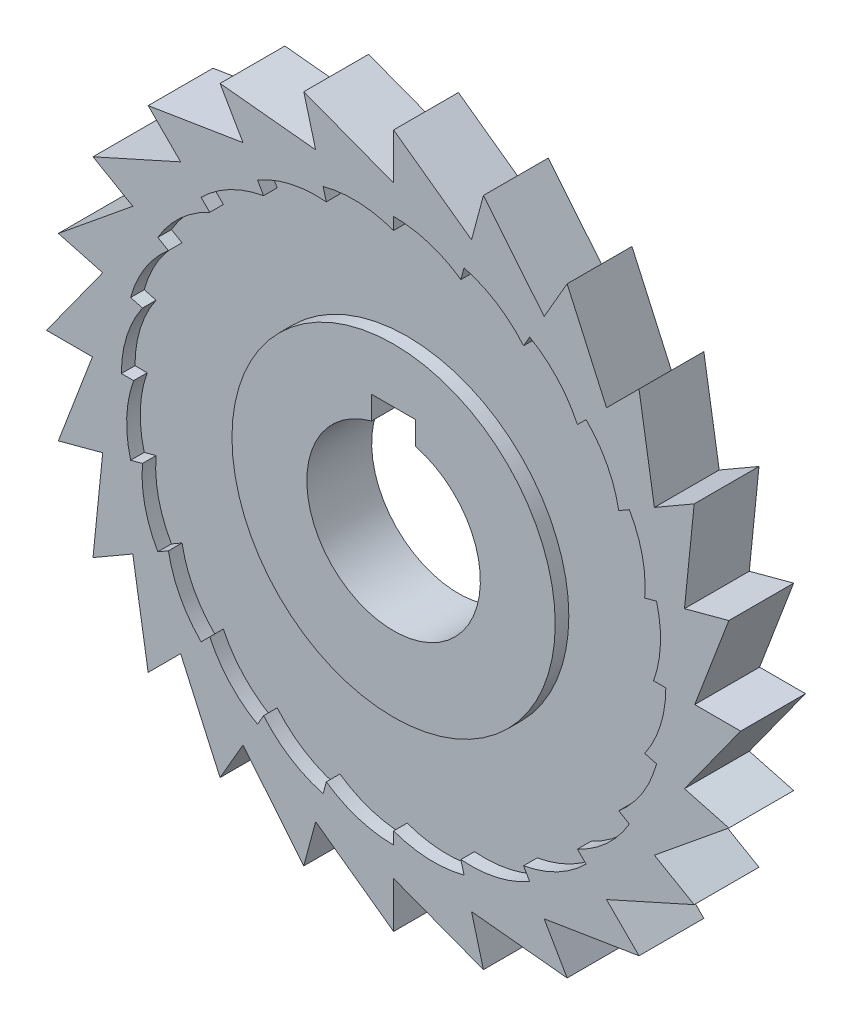
SolidWorks part; units mm, degrees
ref_plane "Alzado" through (0, 0, 0) normal (0, 0, 1) x (1, 0, 0)
ref_plane "Planta" through (0, 0, 0) normal (0, 1, 0) x (1, 0, 0)
ref_plane "Vista lateral" through (0, 0, 0) normal (1, 0, 0) x (0, 0, -1)
sketch "Croquis1" plane through (0, 0, 0) normal (0, 0, 1) x (1, 0, 0)
  line L1 (-3.25, 15.75) -> (3.25, 15.75)
  line L2 (-3.25, 15.75) -> (-3.25, 12.3288)
  line L3 (3.25, 15.75) -> (3.25, 12.3288)
  arc A0 (-3.25, 12.3288) -> (3.25, 12.3288) centre (0, 0) ccw
  circle A1 centre (0, 0) radius 23.75
  circle A2 centre (0, 0) radius 40
  point P9 (0, 15.75)
  dimension "D1" = 25.5
  dimension "D2" = 47.5
  dimension "D3" = 80
  dimension "D4" = 6.5
extrude "Saliente-Extruir1" add sketch "Croquis1" along normal blind 5.525 contours A1 A0 L2 L1 L3 | A2 A1
ref_plane "Plano1" through (0, 0, 2.7625) normal (0, 0, 1) x (1, 0, 0)
sketch "Croquis3" plane through (0, 0, 2.7625) normal (0, 0, 1) x (1, 0, 0)
  line L0 (-3.25, 15.75) -> (-3.25, 12.3288)
  line L1 (-3.25, 15.75) -> (3.25, 15.75)
  line L2 (3.25, 15.75) -> (3.25, 12.3288)
  arc A0 (-3.25, 12.3288) -> (3.25, 12.3288) centre (0, 0) ccw
  circle A1 centre (0, 0) radius 23.75
  dimension "D1" = 47.5
extrude "Saliente-Extruir3" add sketch "Croquis3" along normal blind 4.7625 and the other way blind 4.7625 contours A1 | A0 L2 L1 L0
ref_plane "Plano3" through (0, 0, 2.7625) normal (0, 0, 1) x (1, 0, 0)
sketch "Croquis5" plane through (0, 0, 2.7625) normal (0, 0, 1) x (1, 0, 0)
  line L0 (0, 40) -> (0, 51)
  line L1 (0, 38.2) -> (0, 40)
  line L2 (0, 38.2) -> (0, 63.7631) construction
  line L3 (9.8869, 36.8984) -> (11.4527, 42.7422)
  line L4 (19.1, 33.0822) -> (22.125, 38.3216)
  line L5 (13.1998, 49.2622) -> (22.125, 38.3216)
  line L6 (10.3528, 38.637) -> (13.1998, 49.2622)
  line L7 (27.0115, 27.0115) -> (31.2895, 31.2895)
  line L8 (0, 51) -> (11.4527, 42.7422)
  line L9 (25.5, 44.1673) -> (31.2895, 31.2895)
  line L10 (20, 34.641) -> (25.5, 44.1673)
  line L11 (33.0822, 19.1) -> (38.3216, 22.125)
  line L12 (36.0624, 36.0624) -> (38.3216, 22.125)
  line L13 (28.2843, 28.2843) -> (36.0624, 36.0624)
  line L14 (36.8984, 9.8869) -> (42.7422, 11.4527)
  line L15 (44.1673, 25.5) -> (42.7422, 11.4527)
  line L16 (34.641, 20) -> (44.1673, 25.5)
  line L17 (38.2, 0) -> (44.25, 0)
  line L18 (49.2622, 13.1998) -> (44.25, 0)
  line L19 (38.637, 10.3528) -> (49.2622, 13.1998)
  line L20 (36.8984, -9.8869) -> (42.7422, -11.4527)
  line L21 (51, 0) -> (42.7422, -11.4527)
  line L22 (40, 0) -> (51, 0)
  line L23 (33.0822, -19.1) -> (38.3216, -22.125)
  line L24 (49.2622, -13.1998) -> (38.3216, -22.125)
  line L25 (38.637, -10.3528) -> (49.2622, -13.1998)
  line L26 (27.0115, -27.0115) -> (31.2895, -31.2895)
  line L27 (44.1673, -25.5) -> (31.2895, -31.2895)
  line L28 (34.641, -20) -> (44.1673, -25.5)
  line L29 (19.1, -33.0822) -> (22.125, -38.3216)
  line L30 (36.0624, -36.0624) -> (22.125, -38.3216)
  line L31 (28.2843, -28.2843) -> (36.0624, -36.0624)
  line L32 (9.8869, -36.8984) -> (11.4527, -42.7422)
  line L33 (25.5, -44.1673) -> (11.4527, -42.7422)
  line L34 (20, -34.641) -> (25.5, -44.1673)
  line L35 (0, -38.2) -> (0, -44.25)
  line L36 (13.1998, -49.2622) -> (0, -44.25)
  line L37 (10.3528, -38.637) -> (13.1998, -49.2622)
  line L38 (-9.8869, -36.8984) -> (-11.4527, -42.7422)
  line L39 (0, -51) -> (-11.4527, -42.7422)
  line L40 (0, -40) -> (0, -51)
  line L41 (-19.1, -33.0822) -> (-22.125, -38.3216)
  line L42 (-13.1998, -49.2622) -> (-22.125, -38.3216)
  line L43 (-10.3528, -38.637) -> (-13.1998, -49.2622)
  line L44 (-27.0115, -27.0115) -> (-31.2895, -31.2895)
  line L45 (-25.5, -44.1673) -> (-31.2895, -31.2895)
  line L46 (-20, -34.641) -> (-25.5, -44.1673)
  line L47 (-33.0822, -19.1) -> (-38.3216, -22.125)
  line L48 (-36.0624, -36.0624) -> (-38.3216, -22.125)
  line L49 (-28.2843, -28.2843) -> (-36.0624, -36.0624)
  line L50 (-36.8984, -9.8869) -> (-42.7422, -11.4527)
  line L51 (-44.1673, -25.5) -> (-42.7422, -11.4527)
  line L52 (-34.641, -20) -> (-44.1673, -25.5)
  line L53 (-38.2, 0) -> (-44.25, 0)
  line L54 (-49.2622, -13.1998) -> (-44.25, 0)
  line L55 (-38.637, -10.3528) -> (-49.2622, -13.1998)
  line L56 (-36.8984, 9.8869) -> (-42.7422, 11.4527)
  line L57 (-51, 0) -> (-42.7422, 11.4527)
  line L58 (-40, 0) -> (-51, 0)
  line L59 (-33.0822, 19.1) -> (-38.3216, 22.125)
  line L60 (-49.2622, 13.1998) -> (-38.3216, 22.125)
  line L61 (-38.637, 10.3528) -> (-49.2622, 13.1998)
  line L62 (-27.0115, 27.0115) -> (-31.2895, 31.2895)
  line L63 (-44.1673, 25.5) -> (-31.2895, 31.2895)
  line L64 (-34.641, 20) -> (-44.1673, 25.5)
  line L65 (-19.1, 33.0822) -> (-22.125, 38.3216)
  line L66 (-36.0624, 36.0624) -> (-22.125, 38.3216)
  line L67 (-28.2843, 28.2843) -> (-36.0624, 36.0624)
  line L68 (-9.8869, 36.8984) -> (-11.4527, 42.7422)
  line L69 (-25.5, 44.1673) -> (-11.4527, 42.7422)
  line L70 (-20, 34.641) -> (-25.5, 44.1673)
  line L71 (0, 38.2) -> (0, 44.25)
  line L72 (-13.1998, 49.2622) -> (0, 44.25)
  line L73 (-10.3528, 38.637) -> (-13.1998, 49.2622)
  arc A1 (0, 40) -> (9.8869, 36.8984) centre (0, 22.6913) cw
  arc A2 (10.3528, 38.637) -> (19.1, 33.0822) centre (5.8729, 21.9181) cw
  arc A3 (20, 34.641) -> (27.0115, 27.0115) centre (11.3456, 19.6512) cw
  arc A4 (28.2843, 28.2843) -> (33.0822, 19.1) centre (16.0452, 16.0452) cw
  arc A5 (34.641, 20) -> (36.8984, 9.8869) centre (19.6512, 11.3456) cw
  arc A6 (38.637, 10.3528) -> (38.2, 0) centre (21.9181, 5.8729) cw
  arc A7 (40, 0) -> (36.8984, -9.8869) centre (22.6913, 0) cw
  arc A8 (38.637, -10.3528) -> (33.0822, -19.1) centre (21.9181, -5.8729) cw
  arc A9 (34.641, -20) -> (27.0115, -27.0115) centre (19.6512, -11.3456) cw
  arc A10 (28.2843, -28.2843) -> (19.1, -33.0822) centre (16.0452, -16.0452) cw
  arc A11 (20, -34.641) -> (9.8869, -36.8984) centre (11.3456, -19.6512) cw
  arc A12 (10.3528, -38.637) -> (0, -38.2) centre (5.8729, -21.9181) cw
  arc A13 (0, -40) -> (-9.8869, -36.8984) centre (0, -22.6913) cw
  arc A14 (-10.3528, -38.637) -> (-19.1, -33.0822) centre (-5.8729, -21.9181) cw
  arc A15 (-20, -34.641) -> (-27.0115, -27.0115) centre (-11.3456, -19.6512) cw
  arc A16 (-28.2843, -28.2843) -> (-33.0822, -19.1) centre (-16.0452, -16.0452) cw
  arc A17 (-34.641, -20) -> (-36.8984, -9.8869) centre (-19.6512, -11.3456) cw
  arc A18 (-38.637, -10.3528) -> (-38.2, 0) centre (-21.9181, -5.8729) cw
  arc A19 (-40, 0) -> (-36.8984, 9.8869) centre (-22.6913, 0) cw
  arc A20 (-38.637, 10.3528) -> (-33.0822, 19.1) centre (-21.9181, 5.8729) cw
  arc A21 (-34.641, 20) -> (-27.0115, 27.0115) centre (-19.6512, 11.3456) cw
  arc A22 (-28.2843, 28.2843) -> (-19.1, 33.0822) centre (-16.0452, 16.0452) cw
  arc A23 (-20, 34.641) -> (-9.8869, 36.8984) centre (-11.3456, 19.6512) cw
  arc A24 (-10.3528, 38.637) -> (0, 38.2) centre (-5.8729, 21.9181) cw
  point P125 (0, 0)
  dimension "D1" = 11
  dimension "D2" = 1.8
  dimension "D3" = 14.1194
  dimension "D4" = 24
ref_plane "Plano4" through (0, 51, 0) normal (0, 1, 0) x (1, 0, 0)
sketch "Croquis14" plane through (0, 0, 2.7625) normal (0, 0, 1) x (1, 0, 0)
  line L0 (0, 51) -> (11.4527, 42.7422)
  line L1 (11.4527, 42.7422) -> (9.8869, 36.8984)
  line L2 (0, 51) -> (0, 40)
  arc A0 (0, 40) -> (9.8869, 36.8984) centre (0, 22.6913) cw
sketch "Croquis15" plane through (0, 51, 0) normal (0, 1, 0) x (1, 0, 0)
  line L0 (0, -2.7625) -> (0, 2)
  line L1 (0, -2.7625) -> (0, -7.525)
  dimension "D1" = 4.7625
  dimension "D2" = 4.7625
extrude "Saliente-Extruir9" add sketch "Croquis5" along normal blind 4.7625 and the other way blind 4.7625 contours L0 A1 L3 L8 | L3 A2 L4 L5 L6 | L4 A3 L7 L9 L10 | L7 A4 L11 L12 L13 | L14 A6 L17 L18 L19 | L17 A7 L20 L21 L22 | L20 A8 L23 L24 L25 | L23 A9 L26 L27 L28 | L26 A10 L29 L30 L31 | L29 A11 L32 L33 L34 | L32 A12 L35 L36 L37 | L35 A13 L38 L39 L40 | L38 A14 L41 L42 L43 | L41 A15 L44 L45 L46 | L44 A16 L47 L48 L49 | L47 A17 L50 L51 L52 | L50 A18 L53 L54 L55 | L53 A19 L56 L57 L58 | L62 A22 L65 L66 L67 | L65 A23 L68 L69 L70 | L68 A24 L1 L0 L72 L73 | L60 L59 A20 L61
sketch "Croquis17" plane through (24.1943, 33.5552, 0) normal (0.5849, 0.8111, 0) x (0.8111, -0.5849, 0)
  line L2 (-15.7083, 2) -> (-15.7083, -7.525) construction
  line L5 (-29.8276, 2) -> (-15.7083, 0)
  line L7 (-29.8276, 2) -> (-15.7083, 2)
  line L8 (-15.7083, 2) -> (-15.7083, 0)
  line L9 (-15.7083, -7.525) -> (-15.7083, -5.525)
  line L10 (-29.8276, -7.525) -> (-15.7083, -7.525)
  line L11 (-29.8276, -7.525) -> (-15.7083, -5.525)
